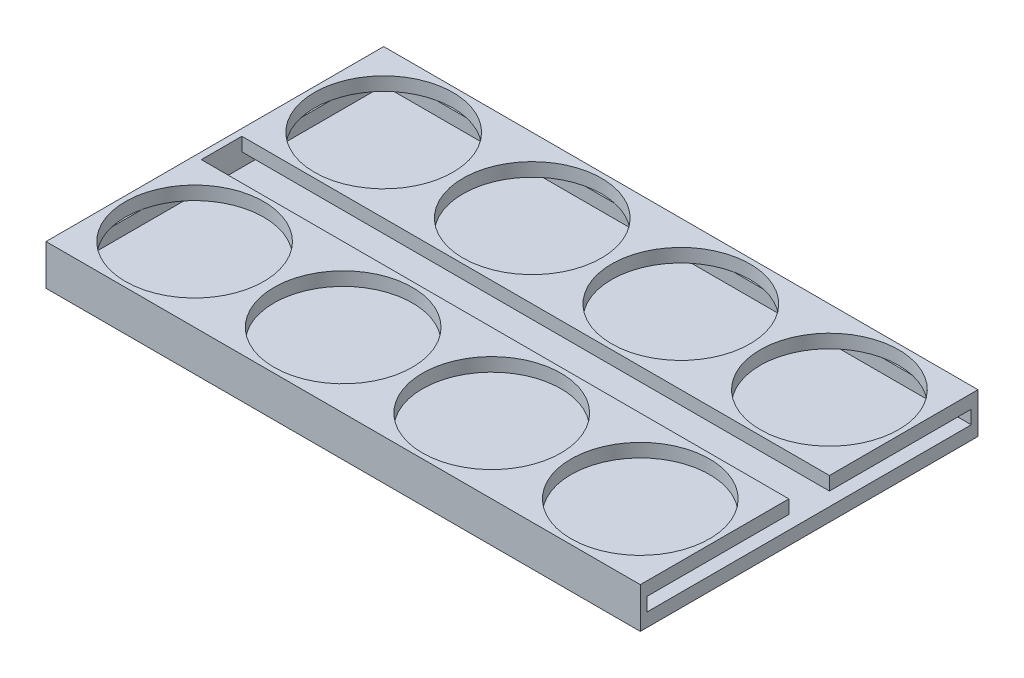
SolidWorks part; units mm, degrees
ref_plane "Front Plane" through (0, 0, 0) normal (0, 0, 1) x (1, 0, 0)
ref_plane "Top Plane" through (0, 0, 0) normal (0, 1, 0) x (1, 0, 0)
ref_plane "Right Plane" through (0, 0, 0) normal (1, 0, 0) x (0, 0, -1)
sketch "Sketch1" plane through (0, 0, 0) normal (0, 1, 0) x (1, 0, 0)
  line L1 (0, 0) -> (88, 0)
  line L2 (0, 0) -> (0, 50)
  line L3 (0, 50) -> (88, 50)
  line L4 (88, 0) -> (88, 50)
  dimension "D1" = 88
  dimension "D2" = 50
extrude "Boss-Extrude1" add sketch "Sketch1" against normal blind 6 contours L3 L4 L1 L2
sketch "Sketch2" plane through (88, 0, 0) normal (1, 0, 0) x (0, 0, -1)
  line L0 (0, -6) -> (0, 0) construction
  line L1 (1, -2) -> (49, -2)
  line L2 (1, -2) -> (1, -4)
  line L3 (1, -4) -> (49, -4)
  line L4 (49, -2) -> (49, -4)
  line L5 (0, 0) -> (50, 0) construction
  line L6 (0, -6) -> (50, -6) construction
  dimension "D1" = 48
  dimension "D2" = 1
  dimension "D3" = 2
  dimension "D4" = 2
extrude "Cut-Extrude1" cut sketch "Sketch2" against normal blind 87
sketch "Sketch3" plane through (0, 0, 0) normal (0, 1, 0) x (1, 0, 0)
  line L0 (88, 0) -> (88, 50) construction
  line L1 (0, 0) -> (88, 0) construction
  circle A0 centre (77, 11) radius 10.25
  dimension "D1" = 20.5
  dimension "D2" = 11
  dimension "D3" = 11
extrude "Cut-Extrude2" cut sketch "Sketch3" against normal blind 2 contours A0
pattern_linear "LPattern1" count 4 spacing 22 along (-1, 0, 0) of "Cut-Extrude2"
sketch "Sketch4" plane through (0, 0, 0) normal (0, 1, 0) x (1, 0, 0)
  line L0 (0, 50) -> (88, 50) construction
  line L1 (88, 0) -> (88, 50) construction
  circle A0 centre (77, 39) radius 10.25
  dimension "D1" = 20.5
  dimension "D2" = 11
  dimension "D3" = 11
extrude "Cut-Extrude3" cut sketch "Sketch4" against normal blind 2
pattern_linear "LPattern2" count 4 spacing 22 along (-1, 0, 0) of "Cut-Extrude3"
sketch "Sketch5" plane through (0, 0, 0) normal (0, 1, 0) x (1, 0, 0)
  line L0 (88, 0) -> (88, 50) construction
  line L1 (1, 22) -> (88, 22)
  line L2 (1, 22) -> (1, 28)
  line L3 (1, 28) -> (88, 28)
  line L4 (88, 22) -> (88, 28)
  circle A0 centre (11, 39) radius 10.25 construction
  dimension "D1" = 87
  dimension "D2" = 6
  dimension "D3" = 11
extrude "Cut-Extrude4" cut sketch "Sketch5" against normal blind 2
